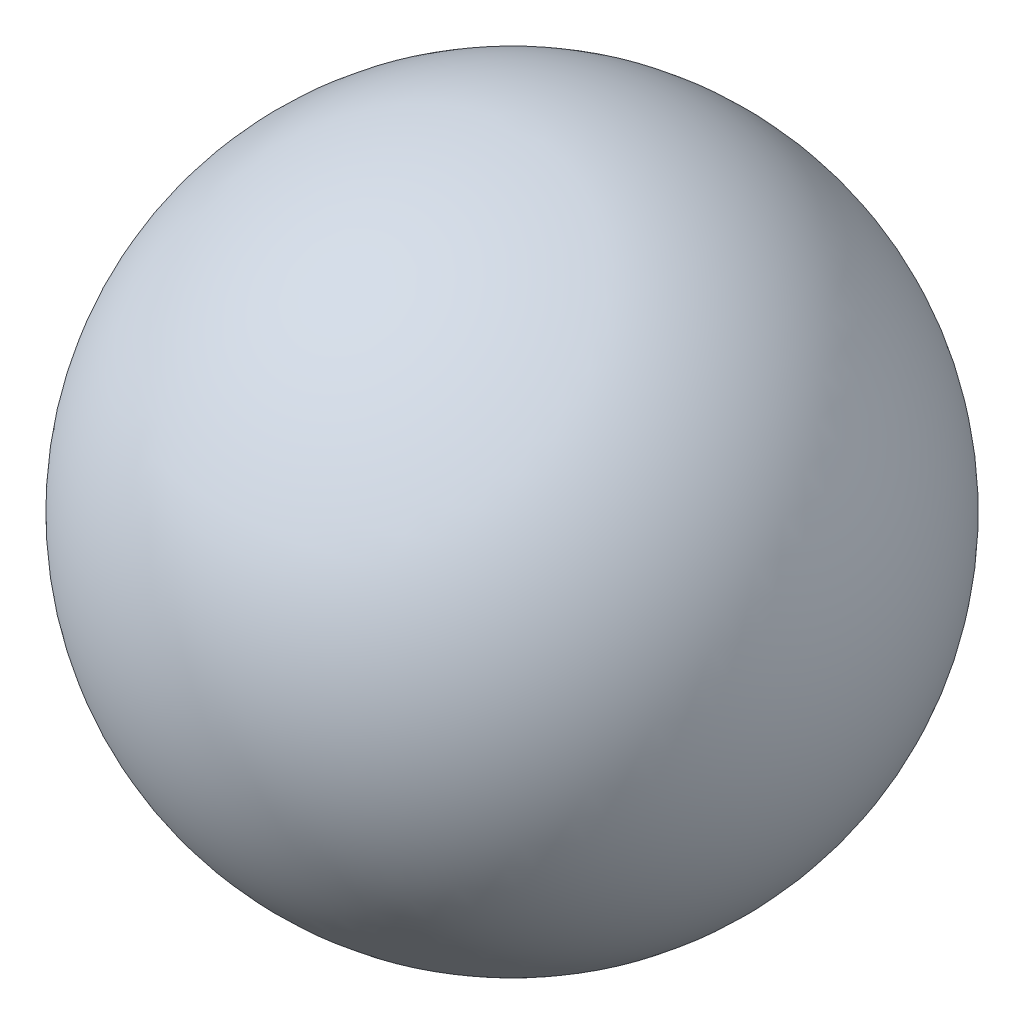
SolidWorks part; units mm, degrees
ref_plane "Front Plane" through (0, 0, 0) normal (0, 0, 1) x (1, 0, 0)
ref_plane "Top Plane" through (0, 0, 0) normal (0, 1, 0) x (1, 0, 0)
ref_plane "Right Plane" through (0, 0, 0) normal (1, 0, 0) x (0, 0, -1)
sketch "Sketch1" plane through (0, 0, 0) normal (0, 0, 1) x (1, 0, 0)
  line L0 (0, 0) -> (0, -11.524) construction
  line L1 (0, -2.262) -> (0, -9.262)
  arc A0 (0, -9.262) -> (0, -2.262) centre (0, -5.762) ccw
  dimension "D1" = 7
revolve "Revolve1" add sketch "Sketch1" angle 360 about L0
